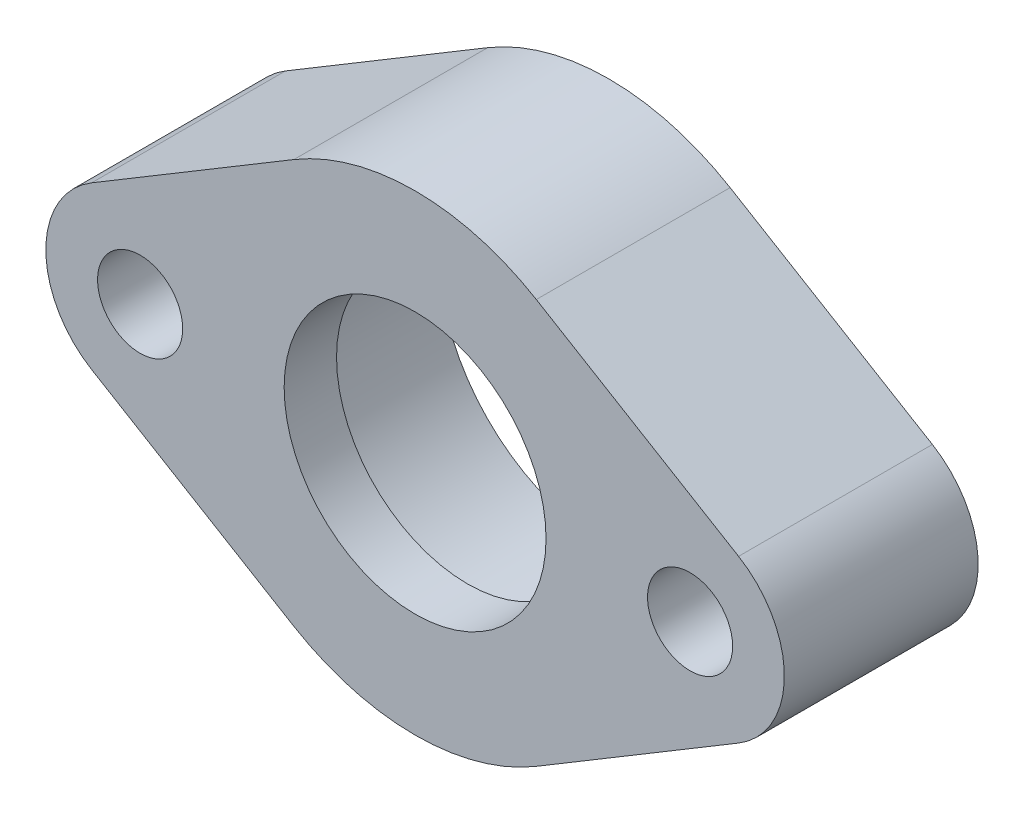
SolidWorks part; units mm, degrees
material "304 SSTL"
ref_plane "XY" through (0, 0, 0) normal (0, 0, 1) x (1, 0, 0)
ref_plane "XZ" through (0, 0, 0) normal (0, 1, 0) x (1, 0, 0)
ref_plane "YZ" through (0, 0, 0) normal (1, 0, 0) x (0, 0, -1)
sketch "Sketch1" plane through (0, 0, 0) normal (0, 0, 1) x (1, 0, 0)
  line L2 (-20.6375, 0) -> (20.6375, 0) construction
  line L3 (0, 20.6375) -> (0, -20.6375) construction
  line L4 (-39.2158, 9.8026) -> (-14.6957, 24.5065)
  line L5 (14.6957, 24.5065) -> (39.2158, 9.8026)
  line L6 (39.2158, -9.8026) -> (14.6957, -24.5065)
  line L7 (-14.6957, -24.5065) -> (-39.2158, -9.8026)
  circle A0 centre (-33.3375, 0) radius 5.1562
  circle A1 centre (33.3375, 0) radius 5.1562
  circle A4 centre (0, 0) radius 20.6375 construction
  arc A5 (-14.6957, -24.5065) -> (14.6957, -24.5065) centre (0, 0) ccw
  arc A6 (14.6957, 24.5065) -> (-14.6957, 24.5065) centre (0, 0) ccw
  arc A7 (39.2158, -9.8026) -> (39.2158, 9.8026) centre (33.3375, 0) ccw
  arc A8 (-39.2158, 9.8026) -> (-39.2158, -9.8026) centre (-33.3375, 0) ccw
  dimension "D1" = 10.3124
  dimension "D2" = 11.43
  dimension "D4" = 41.275
  dimension "D5" = 57.15
  dimension "D3" = 66.675
extrude "Extrude1" add sketch "Sketch1" along normal blind 23.495
sketch "Sketch6" plane through (0, 0, 0) normal (0, 0, 1) x (1, 0, 0)
  circle A0 centre (0, 0) radius 20.6438
  dimension "D1" = 41.2877
extrude "Cut-Extrude1" cut sketch "Sketch6" along normal blind 17.145
sketch "Sketch7" plane through (0, 0, 17.145) normal (0, 0, -1) x (-1, 0, 0)
  circle A0 centre (0, 0) radius 15.875
  dimension "D1" = 31.75
extrude "Cut-Extrude2" cut sketch "Sketch7" against normal through all
fillet "Fillet1" radius 0.127 1 edges at (20.6438, 0, 17.145)
